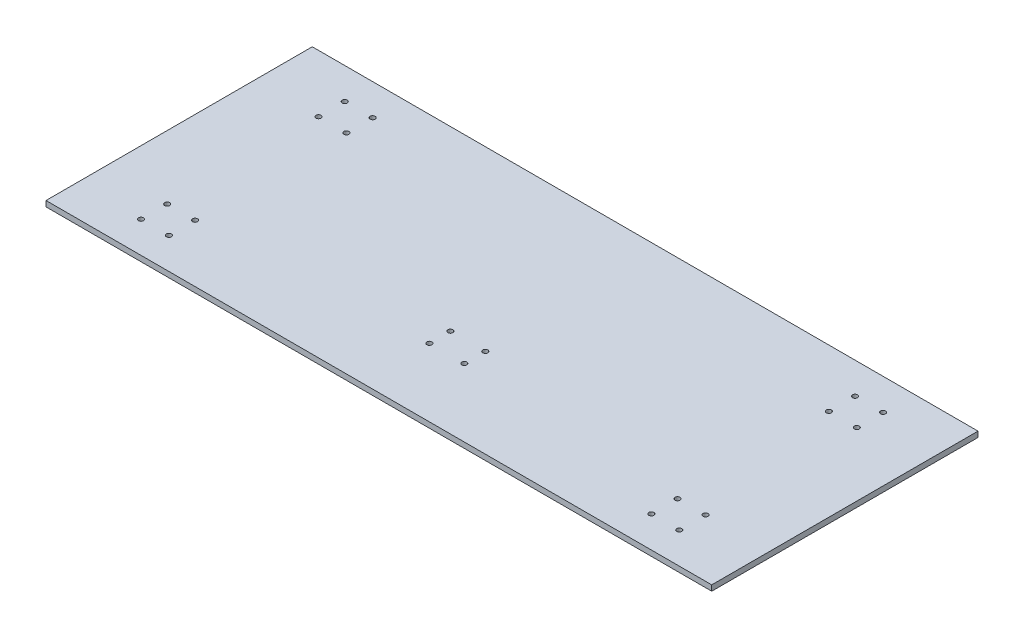
SolidWorks part; units mm, degrees
ref_plane "Front Plane" through (0, 0, 0) normal (0, 0, 1) x (1, 0, 0)
ref_plane "Top Plane" through (0, 0, 0) normal (0, 1, 0) x (1, 0, 0)
ref_plane "Right Plane" through (0, 0, 0) normal (1, 0, 0) x (0, 0, -1)
sketch "Sketch1" plane through (0, 0, 0) normal (0, 1, 0) x (1, 0, 0)
  line L1 (-381, 152.4) -> (381, 152.4)
  line L2 (-381, 152.4) -> (-381, -152.4)
  line L3 (-381, -152.4) -> (381, -152.4)
  line L4 (381, 152.4) -> (381, -152.4)
  line L5 (-381, 152.4) -> (381, -152.4) construction
  line L6 (-381, -152.4) -> (381, 152.4) construction
  point P0 (0, 0)
  dimension "D1" = 304.8
  dimension "D2" = 762
extrude "Boss-Extrude1" add sketch "Sketch1" along normal blind 6.35
ref_plane "Front" through (0, 0, 152.4) normal (0, 0, 1) x (1, 0, 0)
hole_wizard "M5 Clearance Hole1" positions "Sketch4" profile "Sketch5" hole size "M5" standard "ANSI Metric" end condition up to next
sketch "Sketch4" plane through (0, 6.35, 0) normal (0, 1, 0) x (1, 0, 0)
  circle A0 centre (276.1, 116.6) radius 2.1 construction
  circle A1 centre (276.1, 86.6) radius 2.1 construction
  circle A2 centre (308.1, 116.6) radius 2.1 construction
  circle A3 centre (308.1, 86.6) radius 2.1 construction
  circle A4 centre (276.1, -86.6) radius 2.1 construction
  circle A5 centre (276.1, -116.6) radius 2.1 construction
  circle A6 centre (308.1, -86.6) radius 2.1 construction
  circle A7 centre (308.1, -116.6) radius 2.1 construction
  circle A8 centre (-308.1, 116.6) radius 2.1 construction
  circle A9 centre (-308.1, 86.6) radius 2.1 construction
  circle A10 centre (-276.1, 116.6) radius 2.1 construction
  circle A11 centre (-276.1, 86.6) radius 2.1 construction
  circle A12 centre (-276.1, -86.6) radius 2.1 construction
  circle A13 centre (-276.1, -116.6) radius 2.1 construction
  circle A14 centre (-308.1, -116.6) radius 2.1 construction
  circle A15 centre (-308.1, -86.6) radius 2.1 construction
  circle A16 centre (276.1, 116.6) radius 2.1 construction
  circle A17 centre (276.1, 86.6) radius 2.1 construction
  circle A18 centre (308.1, 116.6) radius 2.1 construction
  circle A19 centre (308.1, 86.6) radius 2.1 construction
  circle A20 centre (276.1, -86.6) radius 2.1 construction
  circle A21 centre (276.1, -116.6) radius 2.1 construction
  circle A22 centre (308.1, -86.6) radius 2.1 construction
  circle A23 centre (308.1, -116.6) radius 2.1 construction
  circle A24 centre (-308.1, 116.6) radius 2.1 construction
  circle A25 centre (-308.1, 86.6) radius 2.1 construction
  circle A26 centre (-276.1, 116.6) radius 2.1 construction
  circle A27 centre (-276.1, 86.6) radius 2.1 construction
  circle A28 centre (-276.1, -86.6) radius 2.1 construction
  circle A29 centre (-276.1, -116.6) radius 2.1 construction
  circle A30 centre (-308.1, -116.6) radius 2.1 construction
  circle A31 centre (-308.1, -86.6) radius 2.1 construction
  circle A32 centre (-20, -74.55) radius 2.1 construction
  circle A33 centre (20, -74.55) radius 2.1 construction
  circle A34 centre (20, -50.55) radius 2.1 construction
  circle A35 centre (-20, -50.55) radius 2.1 construction
  circle A36 centre (-20, -74.55) radius 2.1 construction
  circle A37 centre (20, -74.55) radius 2.1 construction
  circle A38 centre (20, -50.55) radius 2.1 construction
  circle A39 centre (-20, -50.55) radius 2.1 construction
  point P1 (276.1, 116.6)
  point P3 (276.1, 86.6)
  point P5 (308.1, 116.6)
  point P7 (308.1, 86.6)
  point P9 (276.1, -86.6)
  point P11 (276.1, -116.6)
  point P13 (308.1, -86.6)
  point P15 (308.1, -116.6)
  point P17 (-308.1, 116.6)
  point P19 (-308.1, 86.6)
  point P21 (-276.1, 116.6)
  point P23 (-276.1, 86.6)
  point P25 (-276.1, -86.6)
  point P27 (-276.1, -116.6)
  point P29 (-308.1, -116.6)
  point P31 (-308.1, -86.6)
  point P63 (20, -50.55)
  point P66 (20, -74.55)
  point P69 (-20, -74.55)
  point P72 (-20, -50.55)
  point P76 (0, 0)
sketch "Sketch5" plane through (276.1, 6.35, -116.6) normal (1, 0, 0) x (0, 0, 1)
  line L0 (0, 0) -> (0, 6.35)
  line L1 (0, 6.35) -> (2.9, 6.35)
  line L2 (2.9, 6.35) -> (2.9, 0)
  line L5 (2.9, 0) -> (0, 0)
  line L11 (0, -6.35) -> (0, 107.95) construction
  dimension "Thru Hole Dia." = 5.8
  dimension "Thru Hole Depth" = 6.35
equation "\"height\"= .25in"
equation "\"width\"= 30in"
equation "\"depth\"= 12in"
equation "\"D1@Sketch1\" = \"depth\""
equation "\"D2@Sketch1\"= \"width\""
equation "\"D1@Boss-Extrude1\"= \"height\""
